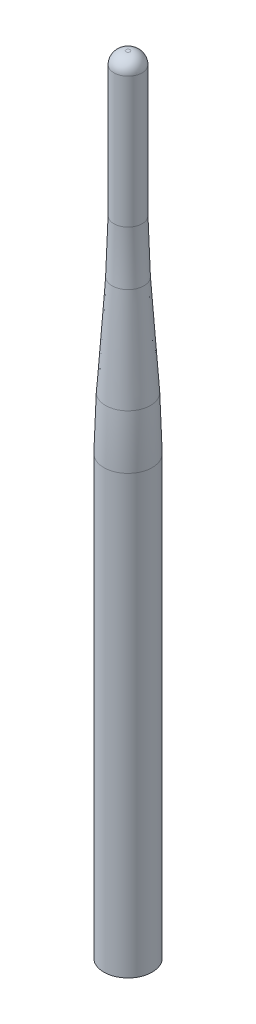
SolidWorks part; units mm, degrees
ref_plane "Płaszczyzna przednia" through (0, 0, 0) normal (0, 0, 1) x (1, 0, 0)
ref_plane "Płaszczyzna górna" through (0, 0, 0) normal (0, 1, 0) x (1, 0, 0)
ref_plane "Płaszczyzna prawa" through (0, 0, 0) normal (1, 0, 0) x (0, 0, -1)
sketch "Sketch1" plane through (0, 0, 0) normal (0, 0, 1) x (1, 0, 0)
  line L0 (0, 0) -> (0, 195)
  line L1 (0, 0) -> (-6, 0)
  line L2 (-6, 0) -> (-6, 108.4282)
  line L5 (-0.5, 195) -> (0, 195)
  line L6 (-3.5, 192) -> (-3.5, 159.5718)
  line L7 (-3.9314, 146.4423) -> (-5.5686, 121.5577)
  arc A0 (-6, 108.4282) -> (-5.5686, 121.5577) centre (194, 108.4282) cw
  arc A1 (-3.5, 159.5718) -> (-3.9314, 146.4423) centre (-203.5, 159.5718) cw
  arc A2 (-3.5, 192) -> (-0.5, 195) centre (-0.5, 192) cw
  point P10 (-6, 115)
  point P13 (-3.5, 153)
  point P16 (-3.5, 195)
  dimension "D6" = 200
  dimension "D7" = 3
  dimension "D1" = 195
  dimension "D2" = 6
  dimension "D3" = 115
  dimension "D4" = 3.5
  dimension "D5" = 42
revolve "Revolve1" add sketch "Sketch1" angle 360 about L0
